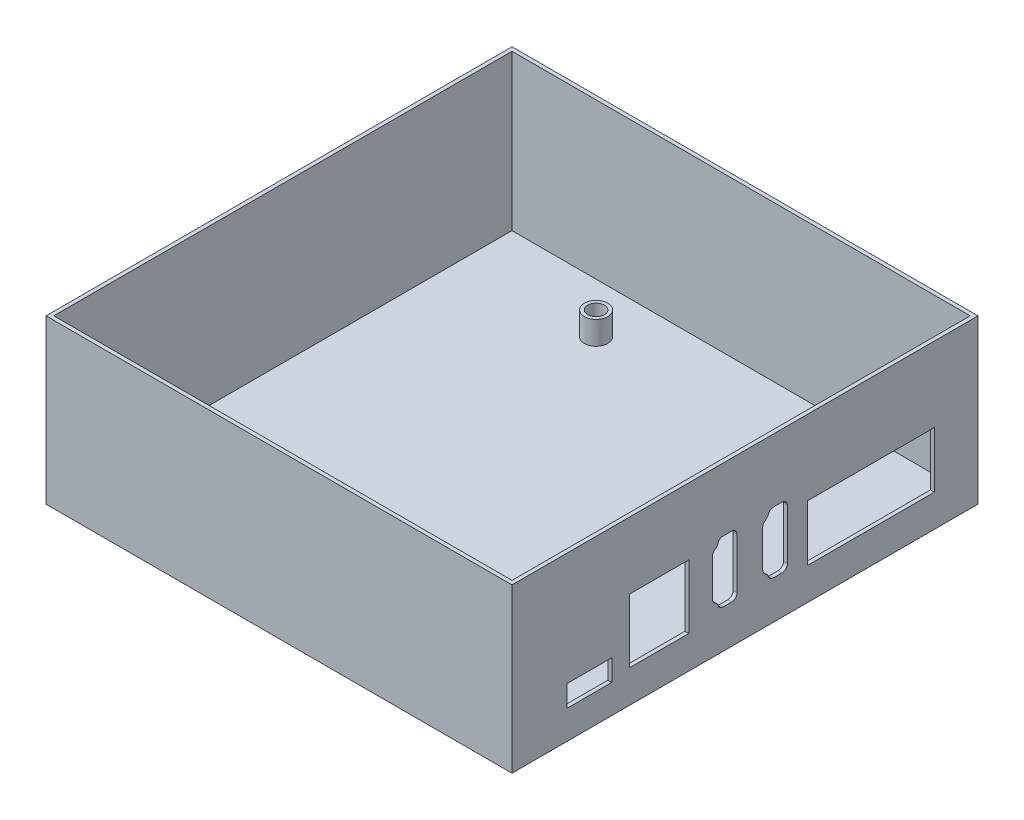
SolidWorks part; units mm, degrees
ref_plane "Front Plane" through (0, 0, 0) normal (0, 0, 1) x (1, 0, 0)
ref_plane "Top Plane" through (0, 0, 0) normal (0, 1, 0) x (1, 0, 0)
ref_plane "Right Plane" through (0, 0, 0) normal (1, 0, 0) x (0, 0, -1)
sketch "Sketch1" plane through (0, 0, 0) normal (0, 1, 0) x (1, 0, 0)
  line L1 (-60, -60) -> (60, -60)
  line L2 (-60, -60) -> (-60, 60)
  line L3 (-60, 60) -> (60, 60)
  line L4 (60, -60) -> (60, 60)
  line L5 (-60, -60) -> (60, 60) construction
  line L6 (-60, 60) -> (60, -60) construction
  point P0 (0, 0)
  dimension "D1" = 120
  dimension "D2" = 120
extrude "Boss-Extrude1" add sketch "Sketch1" along normal blind 2
sketch "Sketch2" plane through (0, 2, 0) normal (0, 1, 0) x (1, 0, 0)
  line L50 (55.5004, 51.6448) -> (-24.4996, 51.6433) construction
  line L51 (59, -44.4664) -> (59, 48.1336) construction
  line L52 (-28.0108, 48.1437) -> (-28.0108, -44.4563) construction
  line L53 (-24.5112, -47.9675) -> (55.4888, -47.966) construction
  line L54 (55.5004, 51.6448) -> (-24.4996, 51.6433)
  line L55 (59, -44.4664) -> (59, 48.1336)
  line L56 (-28.0108, 48.1437) -> (-28.0108, -44.4563)
  line L57 (-24.5112, -47.9675) -> (55.4888, -47.966)
  circle A0 centre (-24.5002, 46.1433) radius 1.5 construction
  circle A1 centre (33.4998, 46.1366) radius 1.5 construction
  circle A2 centre (-24.5411, -42.4487) radius 1.5 construction
  circle A3 centre (33.8018, -42.4555) radius 1.5 construction
  circle A4 centre (-24.5002, 46.1433) radius 1.5
  circle A5 centre (33.4998, 46.1366) radius 1.5
  circle A6 centre (-24.5411, -42.4487) radius 1.5
  circle A7 centre (33.8018, -42.4555) radius 1.5
sketch "Sketch3" plane through (0, 2, 0) normal (0, 1, 0) x (1, 0, 0)
  circle A0 centre (-24.5002, 46.1433) radius 3
  circle A1 centre (33.4998, 46.1366) radius 3
  circle A2 centre (33.8018, -42.4555) radius 3
  circle A3 centre (-24.5411, -42.4487) radius 3
  circle A4 centre (-24.5002, 46.1433) radius 2.15
  circle A5 centre (33.4998, 46.1366) radius 2.15
  circle A6 centre (33.8018, -42.4555) radius 2.15
  circle A7 centre (-24.5411, -42.4487) radius 2.15
  dimension "D1" = 6
  dimension "D2" = 4.3
extrude "Boss-Extrude2" add sketch "Sketch3" along normal blind 6
sketch "Sketch4" plane through (0, 2, 0) normal (0, 1, 0) x (1, 0, 0)
  line L1 (-60, 60) -> (60, 60)
  line L2 (-60, 60) -> (-60, -60)
  line L3 (-60, -60) -> (60, -60)
  line L4 (60, 60) -> (60, -60)
  line L5 (-59, 59) -> (59, 59)
  line L6 (-59, 59) -> (-59, -59)
  line L7 (-59, -59) -> (59, -59)
  line L8 (59, 59) -> (59, -59)
  dimension "D1" = 1
  dimension "D2" = 1
  dimension "D3" = 1
  dimension "D4" = 1
extrude "Boss-Extrude3" add sketch "Sketch4" along normal blind 40
sketch "Sketch5" plane through (60, 0, 0) normal (1, 0, 0) x (0, 0, -1)
  line L0 (5.3577, 12.4049) -> (6.2969, 11.544) construction
  line L1 (6.3247, 11.5004) -> (6.474, 11.0274) construction
  line L2 (7.3323, 10.3984) -> (9.5158, 10.3984) construction
  line L3 (9.5158, 25.1984) -> (7.3323, 25.1984) construction
  line L4 (6.474, 24.5694) -> (6.3247, 24.0965) construction
  line L5 (6.2969, 24.0529) -> (5.3577, 23.1919) construction
  line L6 (5.0658, 22.5285) -> (5.0658, 13.0684) construction
  line L7 (10.4158, 11.2984) -> (10.4158, 24.2984) construction
  line L8 (16.778, 8.7984) -> (32.7546, 8.7984) construction
  line L9 (32.463, 8.7984) -> (48.4396, 8.7984) construction
  line L10 (48.2618, 8.7984) -> (48.2618, 22.1984) construction
  line L11 (48.3634, 22.1984) -> (32.3868, 22.1984) construction
  line L12 (32.6784, 22.1984) -> (16.7018, 22.1984) construction
  line L13 (16.6256, 8.7984) -> (16.6256, 22.1984) construction
  line L14 (5.3577, 12.4049) -> (6.2969, 11.544) construction
  line L15 (6.3247, 11.5004) -> (6.474, 11.0274) construction
  line L16 (7.3323, 10.3984) -> (9.5158, 10.3984) construction
  line L17 (9.5158, 25.1984) -> (7.3323, 25.1984) construction
  line L18 (6.474, 24.5694) -> (6.3247, 24.0965) construction
  line L19 (6.2969, 24.0529) -> (5.3577, 23.1919) construction
  line L20 (5.0658, 22.5285) -> (5.0658, 13.0684) construction
  line L21 (10.4158, 11.2984) -> (10.4158, 24.2984) construction
  line L22 (16.778, 8.7984) -> (32.7546, 8.7984) construction
  line L23 (32.463, 8.7984) -> (48.4396, 8.7984) construction
  line L24 (48.2618, 8.7984) -> (48.2618, 22.1984) construction
  line L25 (48.3634, 22.1984) -> (32.3868, 22.1984) construction
  line L26 (32.6784, 22.1984) -> (16.7018, 22.1984) construction
  line L27 (16.6256, 8.7984) -> (16.6256, 22.1984) construction
  line L28 (-5.6259, 10.3984) -> (-3.4423, 10.3984) construction
  line L29 (-6.6334, 11.5004) -> (-6.4841, 11.0274) construction
  line L30 (-7.6005, 12.4049) -> (-6.6612, 11.544) construction
  line L31 (-7.8923, 22.5285) -> (-7.8923, 13.0684) construction
  line L32 (-6.6612, 24.0529) -> (-7.6005, 23.1919) construction
  line L33 (-6.4841, 24.5694) -> (-6.6334, 24.0965) construction
  line L34 (-3.4423, 25.1984) -> (-5.6259, 25.1984) construction
  line L35 (-2.5423, 11.2984) -> (-2.5423, 24.2984) construction
  line L36 (-5.6259, 10.3984) -> (-3.4423, 10.3984) construction
  line L37 (-6.6334, 11.5004) -> (-6.4841, 11.0274) construction
  line L38 (-7.6005, 12.4049) -> (-6.6612, 11.544) construction
  line L39 (-7.8923, 22.5285) -> (-7.8923, 13.0684) construction
  line L40 (-6.6612, 24.0529) -> (-7.6005, 23.1919) construction
  line L41 (-6.4841, 24.5694) -> (-6.6334, 24.0965) construction
  line L42 (-3.4423, 25.1984) -> (-5.6259, 25.1984) construction
  line L43 (-2.5423, 11.2984) -> (-2.5423, 24.2984) construction
  line L46 (-15.9734, 23.72) -> (-16.6234, 23.72) construction
  line L47 (-15.5734, 9.89) -> (-15.5734, 23.31) construction
  line L48 (-27.6234, 9.48) -> (-27.6234, 9.09)
  line L49 (-27.4234, 8.89) -> (-22.1244, 8.89)
  line L50 (-22.1244, 8.89) -> (-22.1244, 9.48)
  line L51 (-22.1244, 9.48) -> (-27.6234, 9.48)
  line L52 (-27.6234, 9.48) -> (-27.6234, 9.09) construction
  line L53 (-27.4234, 8.89) -> (-22.1244, 8.89) construction
  line L54 (-22.1244, 8.89) -> (-22.1244, 9.48) construction
  line L58 (-15.5634, 17.75) -> (-15.1734, 17.75) construction
  line L59 (-15.3116, 17.79) -> (-15.3116, 15.53) construction
  line L60 (-15.6216, 15.53) -> (-15.3116, 15.53) construction
  line L61 (-15.9216, 15.53) -> (-15.6216, 15.53) construction
  line L62 (-15.1734, 15.45) -> (-15.5634, 15.45) construction
  line L64 (-15.5634, 11.05) -> (-15.1734, 11.05) construction
  line L65 (-15.5634, 9.89) -> (-15.5634, 11.05) construction
  line L66 (-15.9734, 9.48) -> (-16.6234, 9.48) construction
  line L69 (-16.8234, 24.31) -> (-27.4234, 24.31) construction
  line L70 (-16.6234, 23.72) -> (-16.6234, 24.11) construction
  line L71 (-15.9734, 23.72) -> (-16.6234, 23.72) construction
  line L72 (-15.5734, 9.89) -> (-15.5734, 23.31) construction
  line L73 (-15.1734, 22.15) -> (-15.5634, 22.15) construction
  line L74 (-14.9734, 17.95) -> (-14.9734, 21.95) construction
  line L75 (-15.5634, 17.75) -> (-15.1734, 17.75) construction
  line L76 (-15.3116, 17.79) -> (-15.3116, 15.53) construction
  line L77 (-15.6216, 15.53) -> (-15.3116, 15.53) construction
  line L78 (-15.9216, 15.53) -> (-15.6216, 15.53) construction
  line L79 (-15.1734, 15.45) -> (-15.5634, 15.45) construction
  line L80 (-14.9734, 11.25) -> (-14.9734, 15.25) construction
  line L81 (-15.5634, 11.05) -> (-15.1734, 11.05) construction
  line L82 (-15.5634, 9.89) -> (-15.5634, 11.05) construction
  line L83 (-15.9734, 9.48) -> (-16.6234, 9.48) construction
  line L84 (-16.6234, 9.09) -> (-16.6234, 9.48) construction
  line L85 (-22.1224, 8.89) -> (-16.8234, 8.89) construction
  line L86 (-7.078, 24.3491) -> (-7.9383, 23.5605)
  line L87 (-8.3923, 22.5285) -> (-8.3923, 13.0684)
  line L88 (-7.9383, 12.0363) -> (-7.078, 11.2477)
  line L89 (-7.078, 11.2477) -> (-6.9609, 10.8768)
  line L90 (-5.6259, 9.8984) -> (-3.4423, 9.8984)
  line L91 (-2.0423, 11.2984) -> (-2.0423, 24.2984)
  line L92 (-3.4423, 25.6984) -> (-5.6259, 25.6984)
  line L93 (-6.9609, 24.72) -> (-7.078, 24.3491)
  line L94 (5.8801, 24.3491) -> (5.0198, 23.5605)
  line L95 (4.5658, 22.5285) -> (4.5658, 13.0684)
  line L96 (5.0198, 12.0363) -> (5.8801, 11.2477)
  line L97 (5.8801, 11.2477) -> (5.9972, 10.8768)
  line L98 (7.3323, 9.8984) -> (9.5158, 9.8984)
  line L99 (10.9158, 11.2984) -> (10.9158, 24.2984)
  line L100 (9.5158, 25.6984) -> (7.3323, 25.6984)
  line L101 (5.9972, 24.72) -> (5.8801, 24.3491)
  line L102 (-7.9383, 12.0363) -> (-6.9991, 11.1754) construction
  line L103 (16.1256, 22.6984) -> (48.7618, 22.6984)
  line L104 (16.1256, 22.6984) -> (16.1256, 8.2984)
  line L105 (16.1256, 8.2984) -> (48.7618, 8.2984)
  line L106 (48.7618, 22.6984) -> (48.7618, 8.2984)
  line L107 (-7.1102, 11.3498) -> (-6.9609, 10.8768) construction
  line L108 (-6.9609, 24.72) -> (-7.1102, 24.247) construction
  line L109 (-6.9991, 24.4214) -> (-7.9383, 23.5605) construction
  line L110 (5.0198, 12.0363) -> (5.959, 11.1754) construction
  line L111 (5.8479, 11.3498) -> (5.9972, 10.8768) construction
  line L112 (5.9972, 24.72) -> (5.8479, 24.247) construction
  line L113 (5.959, 24.4214) -> (5.0198, 23.5605) construction
  line L114 (-22.1234, 24.31) -> (-22.1244, 9.48) construction
  line L115 (-28.2734, 9.48) -> (-27.6234, 9.48) construction
  line L116 (-28.6834, 9.89) -> (-28.6834, 11.05) construction
  line L119 (-28.6834, 15.45) -> (-29.0734, 15.45) construction
  line L120 (-28.9316, 15.53) -> (-28.6216, 15.53) construction
  line L121 (-28.9316, 15.53) -> (-28.9316, 17.79) construction
  line L122 (-29.0734, 17.75) -> (-28.6834, 17.75) construction
  line L125 (-28.6834, 22.15) -> (-28.6834, 23.31) construction
  line L126 (-28.2734, 23.72) -> (-27.6234, 23.72) construction
  line L127 (-27.6234, 24.11) -> (-27.6234, 23.72) construction
  line L128 (-28.2734, 9.48) -> (-27.6234, 9.48) construction
  line L129 (-28.6834, 9.89) -> (-28.6834, 11.05) construction
  line L130 (-29.0734, 11.05) -> (-28.6834, 11.05) construction
  line L131 (-29.2734, 15.25) -> (-29.2734, 11.25) construction
  line L132 (-28.6834, 15.45) -> (-29.0734, 15.45) construction
  line L133 (-28.9316, 15.53) -> (-28.6216, 15.53) construction
  line L134 (-28.9316, 15.53) -> (-28.9316, 17.79) construction
  line L135 (-29.0734, 17.75) -> (-28.6834, 17.75) construction
  line L136 (-29.2734, 21.95) -> (-29.2734, 17.95) construction
  line L137 (-28.6834, 22.15) -> (-29.0734, 22.15) construction
  line L138 (-28.6834, 22.15) -> (-28.6834, 23.31) construction
  line L139 (-28.2734, 23.72) -> (-27.6234, 23.72) construction
  line L140 (-27.6234, 24.11) -> (-27.6234, 23.72) construction
  line L141 (-15.1734, 23.15) -> (-15.1734, 25.31) construction
  line L142 (-16.4092, 25.31) -> (-27.4234, 25.31) construction
  line L143 (-36.785, 8.7984) -> (-37.547, 8.7984) construction
  line L144 (-15.1734, 25.31) -> (-16.4092, 25.31) construction
  line L145 (-29.7734, 24.81) -> (-14.4734, 24.81)
  line L146 (-29.7734, 24.81) -> (-29.7734, 8.39)
  line L147 (-29.7734, 8.39) -> (-14.4734, 8.39)
  line L148 (-15.6234, 9.09) -> (-15.6234, 9.48) construction
  line L149 (-28.6234, 9.48) -> (-28.6234, 9.09) construction
  line L150 (-27.4234, 7.89) -> (-22.1244, 7.89) construction
  line L152 (-30.2734, 15.6642) -> (-30.2734, 11.25) construction
  line L153 (-28.6234, 9.48) -> (-29.0734, 9.48) construction
  line L154 (-30.2734, 17.5358) -> (-30.2734, 15.6642) construction
  line L155 (-29.0734, 23.15) -> (-29.0734, 25.31) construction
  line L156 (-30.2734, 21.95) -> (-30.2734, 17.5358) construction
  line L157 (-29.0734, 25.31) -> (-27.4234, 25.31) construction
  line L158 (-14.4734, 24.81) -> (-14.4734, 8.39)
  line L159 (-42.565, 8.7984) -> (-43.327, 8.7984) construction
  line L160 (-15.6234, 9.48) -> (-15.1734, 9.48) construction
  line L161 (-15.1734, 9.48) -> (-15.1734, 10.05) construction
  line L162 (-29.0734, 9.48) -> (-29.0734, 10.05) construction
  line L163 (-36.785, 8.7984) -> (-37.547, 8.7984)
  line L164 (-42.565, 8.7984) -> (-43.327, 8.7984)
  line L165 (-42.565, 8.7984) -> (-37.547, 8.7984) construction
  line L166 (-45.806, 12.8984) -> (-34.306, 12.8984)
  line L167 (-45.806, 12.8984) -> (-45.806, 7.3984)
  line L168 (-45.806, 7.3984) -> (-34.306, 7.3984)
  line L169 (-34.306, 12.8984) -> (-34.306, 7.3984)
  arc A0 (-27.6234, 9.09) -> (-27.4234, 8.89) centre (-27.4234, 9.09) ccw
  arc A1 (-27.6234, 9.09) -> (-27.4234, 8.89) centre (-27.4234, 9.09) ccw construction
  arc A2 (-28.6234, 9.09) -> (-27.4234, 7.89) centre (-27.4234, 9.09) ccw construction
  spline S0 degree 3 poles (5.0658, 13.0684) (5.0658, 12.8123) (5.1689, 12.5779) (5.3577, 12.4049) knots 0 0 0 0 1 1 1 1 weights 1 0.943565 0.943565 1 construction
  spline S1 degree 3 poles (6.474, 11.0274) (6.5967, 10.6391) (6.9251, 10.3984) (7.3323, 10.3984) knots 0 0 0 0 1 1 1 1 weights 1 0.871051 0.871051 1 construction
  spline S2 degree 3 poles (9.5158, 10.3984) (10.043, 10.3984) (10.4158, 10.7712) (10.4158, 11.2984) knots 0 0 0 0 1 1 1 1 weights 1 0.804738 0.804738 1 construction
  spline S3 degree 3 poles (10.4158, 24.2984) (10.4158, 24.8256) (10.043, 25.1984) (9.5158, 25.1984) knots 0 0 0 0 1 1 1 1 weights 1 0.804738 0.804738 1 construction
  spline S4 degree 3 poles (7.3323, 25.1984) (6.9251, 25.1984) (6.5967, 24.9577) (6.474, 24.5694) knots 0 0 0 0 1 1 1 1 weights 1 0.871051 0.871051 1 construction
  spline S5 degree 3 poles (5.3577, 23.1919) (5.1689, 23.0189) (5.0658, 22.7845) (5.0658, 22.5285) knots 0 0 0 0 1 1 1 1 weights 1 0.943565 0.943565 1 construction
  spline S6 degree 3 poles (5.0658, 13.0684) (5.0658, 12.8123) (5.1689, 12.5779) (5.3577, 12.4049) knots 0 0 0 0 1 1 1 1 weights 1 0.943565 0.943565 1 construction
  spline S7 degree 3 poles (6.474, 11.0274) (6.5967, 10.6391) (6.9251, 10.3984) (7.3323, 10.3984) knots 0 0 0 0 1 1 1 1 weights 1 0.871051 0.871051 1 construction
  spline S8 degree 3 poles (9.5158, 10.3984) (10.043, 10.3984) (10.4158, 10.7712) (10.4158, 11.2984) knots 0 0 0 0 1 1 1 1 weights 1 0.804738 0.804738 1 construction
  spline S9 degree 3 poles (10.4158, 24.2984) (10.4158, 24.8256) (10.043, 25.1984) (9.5158, 25.1984) knots 0 0 0 0 1 1 1 1 weights 1 0.804738 0.804738 1 construction
  spline S10 degree 3 poles (7.3323, 25.1984) (6.9251, 25.1984) (6.5967, 24.9577) (6.474, 24.5694) knots 0 0 0 0 1 1 1 1 weights 1 0.871051 0.871051 1 construction
  spline S11 degree 3 poles (5.3577, 23.1919) (5.1689, 23.0189) (5.0658, 22.7845) (5.0658, 22.5285) knots 0 0 0 0 1 1 1 1 weights 1 0.943565 0.943565 1 construction
  spline S12 degree 3 poles (-3.4423, 10.3984) (-2.9151, 10.3984) (-2.5423, 10.7712) (-2.5423, 11.2984) knots 0 0 0 0 1 1 1 1 weights 1 0.804738 0.804738 1 construction
  spline S13 degree 3 poles (-6.4841, 11.0274) (-6.3615, 10.6391) (-6.033, 10.3984) (-5.6259, 10.3984) knots 0 0 0 0 1 1 1 1 weights 1 0.871051 0.871051 1 construction
  spline S14 degree 3 poles (-7.8923, 13.0684) (-7.8923, 12.8123) (-7.7892, 12.5779) (-7.6005, 12.4049) knots 0 0 0 0 1 1 1 1 weights 1 0.943565 0.943565 1 construction
  spline S15 degree 3 poles (-7.6005, 23.1919) (-7.7892, 23.0189) (-7.8923, 22.7845) (-7.8923, 22.5285) knots 0 0 0 0 1 1 1 1 weights 1 0.943565 0.943565 1 construction
  spline S16 degree 3 poles (-5.6259, 25.1984) (-6.033, 25.1984) (-6.3615, 24.9577) (-6.4841, 24.5694) knots 0 0 0 0 1 1 1 1 weights 1 0.871051 0.871051 1 construction
  spline S17 degree 3 poles (-2.5423, 24.2984) (-2.5423, 24.8256) (-2.9151, 25.1984) (-3.4423, 25.1984) knots 0 0 0 0 1 1 1 1 weights 1 0.804738 0.804738 1 construction
  spline S18 degree 3 poles (-3.4423, 10.3984) (-2.9151, 10.3984) (-2.5423, 10.7712) (-2.5423, 11.2984) knots 0 0 0 0 1 1 1 1 weights 1 0.804738 0.804738 1 construction
  spline S19 degree 3 poles (-6.4841, 11.0274) (-6.3615, 10.6391) (-6.033, 10.3984) (-5.6259, 10.3984) knots 0 0 0 0 1 1 1 1 weights 1 0.871051 0.871051 1 construction
  spline S20 degree 3 poles (-7.8923, 13.0684) (-7.8923, 12.8123) (-7.7892, 12.5779) (-7.6005, 12.4049) knots 0 0 0 0 1 1 1 1 weights 1 0.943565 0.943565 1 construction
  spline S21 degree 3 poles (-7.6005, 23.1919) (-7.7892, 23.0189) (-7.8923, 22.7845) (-7.8923, 22.5285) knots 0 0 0 0 1 1 1 1 weights 1 0.943565 0.943565 1 construction
  spline S22 degree 3 poles (-5.6259, 25.1984) (-6.033, 25.1984) (-6.3615, 24.9577) (-6.4841, 24.5694) knots 0 0 0 0 1 1 1 1 weights 1 0.871051 0.871051 1 construction
  spline S23 degree 3 poles (-2.5423, 24.2984) (-2.5423, 24.8256) (-2.9151, 25.1984) (-3.4423, 25.1984) knots 0 0 0 0 1 1 1 1 weights 1 0.804738 0.804738 1 construction
  spline S24 degree 3 poles (-16.6234, 24.11) (-16.6234, 24.2272) (-16.7063, 24.31) (-16.8234, 24.31) knots 0 0 0 0 1 1 1 1 weights 1 0.804738 0.804738 1 construction
  spline S25 degree 3 poles (-15.9734, 23.71) (-15.7391, 23.71) (-15.5734, 23.5443) (-15.5734, 23.31) knots 0 0 0 0 1 1 1 1 weights 1 0.804738 0.804738 1 construction
  spline S26 degree 3 poles (-14.9734, 21.95) (-14.9734, 22.0672) (-15.0563, 22.15) (-15.1734, 22.15) knots 0 0 0 0 1 1 1 1 weights 1 0.804738 0.804738 1 construction
  spline S27 degree 3 poles (-15.1734, 17.75) (-15.0563, 17.75) (-14.9734, 17.8328) (-14.9734, 17.95) knots 0 0 0 0 1 1 1 1 weights 1 0.804738 0.804738 1 construction
  spline S28 degree 3 poles (-14.9734, 15.25) (-14.9734, 15.3672) (-15.0563, 15.45) (-15.1734, 15.45) knots 0 0 0 0 1 1 1 1 weights 1 0.804738 0.804738 1 construction
  spline S29 degree 3 poles (-15.1734, 11.05) (-15.0563, 11.05) (-14.9734, 11.1328) (-14.9734, 11.25) knots 0 0 0 0 1 1 1 1 weights 1 0.804738 0.804738 1 construction
  spline S30 degree 3 poles (-15.5734, 9.89) (-15.5734, 9.6557) (-15.7391, 9.49) (-15.9734, 9.49) knots 0 0 0 0 1 1 1 1 weights 1 0.804738 0.804738 1 construction
  spline S31 degree 3 poles (-16.8234, 8.89) (-16.7063, 8.89) (-16.6234, 8.9728) (-16.6234, 9.09) knots 0 0 0 0 1 1 1 1 weights 1 0.804738 0.804738 1 construction
  spline S32 degree 3 poles (-16.6234, 24.11) (-16.6234, 24.2272) (-16.7063, 24.31) (-16.8234, 24.31) knots 0 0 0 0 1 1 1 1 weights 1 0.804738 0.804738 1 construction
  spline S33 degree 3 poles (-15.9734, 23.71) (-15.7391, 23.71) (-15.5734, 23.5443) (-15.5734, 23.31) knots 0 0 0 0 1 1 1 1 weights 1 0.804738 0.804738 1 construction
  spline S34 degree 3 poles (-14.9734, 21.95) (-14.9734, 22.0672) (-15.0563, 22.15) (-15.1734, 22.15) knots 0 0 0 0 1 1 1 1 weights 1 0.804738 0.804738 1 construction
  spline S35 degree 3 poles (-15.1734, 17.75) (-15.0563, 17.75) (-14.9734, 17.8328) (-14.9734, 17.95) knots 0 0 0 0 1 1 1 1 weights 1 0.804738 0.804738 1 construction
  spline S36 degree 3 poles (-14.9734, 15.25) (-14.9734, 15.3672) (-15.0563, 15.45) (-15.1734, 15.45) knots 0 0 0 0 1 1 1 1 weights 1 0.804738 0.804738 1 construction
  spline S37 degree 3 poles (-15.1734, 11.05) (-15.0563, 11.05) (-14.9734, 11.1328) (-14.9734, 11.25) knots 0 0 0 0 1 1 1 1 weights 1 0.804738 0.804738 1 construction
  spline S38 degree 3 poles (-15.5734, 9.89) (-15.5734, 9.6557) (-15.7391, 9.49) (-15.9734, 9.49) knots 0 0 0 0 1 1 1 1 weights 1 0.804738 0.804738 1 construction
  spline S39 degree 3 poles (-16.8234, 8.89) (-16.7063, 8.89) (-16.6234, 8.9728) (-16.6234, 9.09) knots 0 0 0 0 1 1 1 1 weights 1 0.804738 0.804738 1 construction
  spline S40 degree 1 poles (-7.9383, 23.5605) (-8.3923, 22.5285) knots 0 0 1 1 construction
  spline S41 degree 1 poles (-8.3923, 13.0684) (-7.9383, 12.0363) knots 0 0 1 1 construction
  spline S42 degree 3 poles (-7.9383, 23.5605) (-8.0087, 23.496) (-8.1357, 23.3536) (-8.2835, 23.0965) (-8.3732, 22.8137) (-8.3923, 22.6239) (-8.3923, 22.5285) knots 0 0 0 0 0.25 0.5 0.75 1 1 1 1
  spline S43 degree 3 poles (-8.3923, 13.0684) (-8.3923, 12.9729) (-8.3732, 12.7831) (-8.2835, 12.5004) (-8.1357, 12.2432) (-8.0087, 12.1009) (-7.9383, 12.0363) knots 0 0 0 0 0.25 0.5 0.75 1 1 1 1
  spline S44 degree 1 poles (-6.9609, 10.8768) (-5.6259, 9.8984) knots 0 0 1 1 construction
  spline S45 degree 1 poles (-3.4423, 9.8984) (-2.0423, 11.2984) knots 0 0 1 1 construction
  spline S46 degree 1 poles (-2.0423, 24.2984) (-3.4423, 25.6984) knots 0 0 1 1 construction
  spline S47 degree 1 poles (-5.6259, 25.6984) (-6.9609, 24.72) knots 0 0 1 1 construction
  spline S48 degree 3 poles (-6.9609, 10.8768) (-6.9178, 10.7403) (-6.7929, 10.4836) (-6.4691, 10.1479) (-6.0514, 9.9402) (-5.7691, 9.8984) (-5.6259, 9.8984) knots 0 0 0 0 0.25 0.5 0.75 1 1 1 1
  spline S49 degree 3 poles (-3.4423, 9.8984) (-3.2674, 9.8984) (-2.9255, 9.9586) (-2.4216, 10.2777) (-2.1025, 10.7816) (-2.0423, 11.1235) (-2.0423, 11.2984) knots 0 0 0 0 0.25 0.5 0.75 1 1 1 1
  spline S50 degree 3 poles (-2.0423, 24.2984) (-2.0423, 24.4733) (-2.1025, 24.8153) (-2.4216, 25.3192) (-2.9255, 25.6383) (-3.2674, 25.6984) (-3.4423, 25.6984) knots 0 0 0 0 0.25 0.5 0.75 1 1 1 1
  spline S51 degree 3 poles (-5.6259, 25.6984) (-5.7691, 25.6984) (-6.0514, 25.6567) (-6.4691, 25.449) (-6.7929, 25.1132) (-6.9178, 24.8566) (-6.9609, 24.72) knots 0 0 0 0 0.25 0.5 0.75 1 1 1 1
  spline S52 degree 1 poles (5.0198, 23.5605) (4.5658, 22.5285) knots 0 0 1 1 construction
  spline S53 degree 1 poles (4.5658, 13.0684) (5.0198, 12.0363) knots 0 0 1 1 construction
  spline S54 degree 3 poles (5.0198, 23.5605) (4.9494, 23.496) (4.8225, 23.3536) (4.6746, 23.0965) (4.585, 22.8137) (4.5658, 22.6239) (4.5658, 22.5285) knots 0 0 0 0 0.25 0.5 0.75 1 1 1 1
  spline S55 degree 3 poles (4.5658, 13.0684) (4.5658, 12.9729) (4.585, 12.7831) (4.6746, 12.5004) (4.8225, 12.2432) (4.9494, 12.1009) (5.0198, 12.0363) knots 0 0 0 0 0.25 0.5 0.75 1 1 1 1
  spline S56 degree 1 poles (5.9972, 10.8768) (7.3323, 9.8984) knots 0 0 1 1 construction
  spline S57 degree 1 poles (9.5158, 9.8984) (10.9158, 11.2984) knots 0 0 1 1 construction
  spline S58 degree 1 poles (10.9158, 24.2984) (9.5158, 25.6984) knots 0 0 1 1 construction
  spline S59 degree 1 poles (7.3323, 25.6984) (5.9972, 24.72) knots 0 0 1 1 construction
  spline S60 degree 3 poles (5.9972, 10.8768) (6.0404, 10.7403) (6.1652, 10.4836) (6.489, 10.1479) (6.9067, 9.9402) (7.189, 9.8984) (7.3323, 9.8984) knots 0 0 0 0 0.25 0.5 0.75 1 1 1 1
  spline S61 degree 3 poles (9.5158, 9.8984) (9.6907, 9.8984) (10.0327, 9.9586) (10.5366, 10.2777) (10.8557, 10.7816) (10.9158, 11.1235) (10.9158, 11.2984) knots 0 0 0 0 0.25 0.5 0.75 1 1 1 1
  spline S62 degree 3 poles (10.9158, 24.2984) (10.9158, 24.4733) (10.8557, 24.8153) (10.5366, 25.3192) (10.0327, 25.6383) (9.6907, 25.6984) (9.5158, 25.6984) knots 0 0 0 0 0.25 0.5 0.75 1 1 1 1
  spline S63 degree 3 poles (7.3323, 25.6984) (7.189, 25.6984) (6.9067, 25.6567) (6.489, 25.449) (6.1652, 25.1132) (6.0404, 24.8566) (5.9972, 24.72) knots 0 0 0 0 0.25 0.5 0.75 1 1 1 1
  spline S64 degree 3 poles (-28.2734, 9.49) (-28.5077, 9.49) (-28.6734, 9.6557) (-28.6734, 9.89) knots 0 0 0 0 1 1 1 1 weights 1 0.804738 0.804738 1 construction
  spline S65 degree 3 poles (-29.2734, 11.25) (-29.2734, 11.1328) (-29.1906, 11.05) (-29.0734, 11.05) knots 0 0 0 0 1 1 1 1 weights 1 0.804738 0.804738 1 construction
  spline S66 degree 3 poles (-29.0734, 15.45) (-29.1906, 15.45) (-29.2734, 15.3672) (-29.2734, 15.25) knots 0 0 0 0 1 1 1 1 weights 1 0.804738 0.804738 1 construction
  spline S67 degree 3 poles (-29.2734, 17.95) (-29.2734, 17.8328) (-29.1906, 17.75) (-29.0734, 17.75) knots 0 0 0 0 1 1 1 1 weights 1 0.804738 0.804738 1 construction
  spline S68 degree 3 poles (-29.0734, 22.15) (-29.1906, 22.15) (-29.2734, 22.0672) (-29.2734, 21.95) knots 0 0 0 0 1 1 1 1 weights 1 0.804738 0.804738 1 construction
  spline S69 degree 3 poles (-28.6734, 23.31) (-28.6734, 23.5443) (-28.5077, 23.71) (-28.2734, 23.71) knots 0 0 0 0 1 1 1 1 weights 1 0.804738 0.804738 1 construction
  spline S70 degree 3 poles (-27.6234, 23.4102) (-27.6234, 23.4159) (-27.6234, 23.543) (-27.6234, 23.72) knots 0 0 0 0 1 1 1 1 weights 1 0.812281 0.812281 1 construction
  spline S71 degree 3 poles (-27.4234, 24.31) (-27.5406, 24.31) (-27.6234, 24.2272) (-27.6234, 24.11) knots 0 0 0 0 1 1 1 1 weights 1 0.804738 0.804738 1 construction
  spline S72 degree 3 poles (-28.2734, 9.49) (-28.5077, 9.49) (-28.6734, 9.6557) (-28.6734, 9.89) knots 0 0 0 0 1 1 1 1 weights 1 0.804738 0.804738 1 construction
  spline S73 degree 3 poles (-29.2734, 11.25) (-29.2734, 11.1328) (-29.1906, 11.05) (-29.0734, 11.05) knots 0 0 0 0 1 1 1 1 weights 1 0.804738 0.804738 1 construction
  spline S74 degree 3 poles (-29.0734, 15.45) (-29.1906, 15.45) (-29.2734, 15.3672) (-29.2734, 15.25) knots 0 0 0 0 1 1 1 1 weights 1 0.804738 0.804738 1 construction
  spline S75 degree 3 poles (-29.2734, 17.95) (-29.2734, 17.8328) (-29.1906, 17.75) (-29.0734, 17.75) knots 0 0 0 0 1 1 1 1 weights 1 0.804738 0.804738 1 construction
  spline S76 degree 3 poles (-29.0734, 22.15) (-29.1906, 22.15) (-29.2734, 22.0672) (-29.2734, 21.95) knots 0 0 0 0 1 1 1 1 weights 1 0.804738 0.804738 1 construction
  spline S77 degree 3 poles (-28.6734, 23.31) (-28.6734, 23.5443) (-28.5077, 23.71) (-28.2734, 23.71) knots 0 0 0 0 1 1 1 1 weights 1 0.804738 0.804738 1 construction
  spline S78 degree 3 poles (-27.6234, 23.4102) (-27.6234, 23.4159) (-27.6234, 23.543) (-27.6234, 23.72) knots 0 0 0 0 1 1 1 1 weights 1 0.812281 0.812281 1 construction
  spline S79 degree 3 poles (-27.4234, 24.31) (-27.5406, 24.31) (-27.6234, 24.2272) (-27.6234, 24.11) knots 0 0 0 0 1 1 1 1 weights 1 0.804738 0.804738 1 construction
  spline S85 degree 3 poles (-13.9734, 21.95) (-13.9734, 22.0999) (-14.025, 22.393) (-14.2985, 22.8249) (-14.7304, 23.0984) (-15.0236, 23.15) (-15.1734, 23.15) knots 0 0 0 0 0.25 0.5 0.75 1 1 1 1 construction
  spline S91 degree 3 poles (-16.8234, 7.89) (-16.6736, 7.89) (-16.3804, 7.9416) (-15.9485, 8.2151) (-15.675, 8.647) (-15.6234, 8.9401) (-15.6234, 9.09) knots 0 0 0 0 0.25 0.5 0.75 1 1 1 1 construction
  spline S95 degree 3 poles (-30.2734, 11.25) (-30.2734, 11.1001) (-30.2219, 10.807) (-29.9484, 10.3751) (-29.5165, 10.1016) (-29.2233, 10.05) (-29.0734, 10.05) knots 0 0 0 0 0.25 0.5 0.75 1 1 1 1 construction
  spline S98 degree 3 poles (-29.0734, 23.15) (-29.2233, 23.15) (-29.5165, 23.0984) (-29.9484, 22.8249) (-30.2219, 22.393) (-30.2734, 22.0999) (-30.2734, 21.95) knots 0 0 0 0 0.25 0.5 0.75 1 1 1 1 construction
  point P134 (-40.056, 8.7984)
  point P177 (-40.056, 12.8984)
  point P178 (-45.806, 10.1484)
  dimension "D4" = 0.5
  dimension "D5" = 0.5
  dimension "D6" = 0.5
  dimension "D7" = 0.5
  dimension "D8" = 0.5
  dimension "D9" = 0.5
  dimension "D10" = 0.5
  dimension "D11" = 0.5
  dimension "D12" = 11.5
  dimension "D13" = 1.35
  dimension "D14" = 5.5
  dimension "D1" = 0
  dimension "D2" = 0.5
  dimension "D3" = 0.5
extrude "Cut-Extrude1" cut sketch "Sketch5" against normal up to surface (1 mm away)
